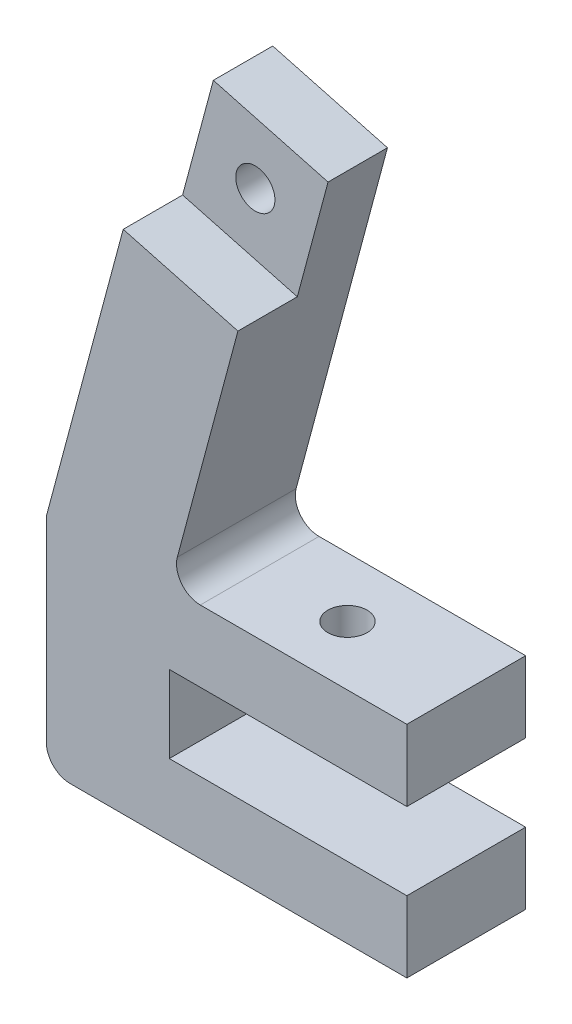
SolidWorks part; units mm, degrees
ref_plane "前视基准面" through (0, 0, 0) normal (0, 0, 1) x (1, 0, 0)
ref_plane "上视基准面" through (0, 0, 0) normal (0, 1, 0) x (1, 0, 0)
ref_plane "右视基准面" through (0, 0, 0) normal (1, 0, 0) x (0, 0, -1)
other "Configuration Table"
sketch "草图1" plane through (0, 0, 0) normal (0, 0, 1) x (1, 0, 0)
  line L0 (0, 0) -> (0, 6)
  line L1 (0, 6) -> (-20, 6)
  line L2 (-20, 6) -> (-20, 12.5)
  line L3 (-20, 12.5) -> (0, 12.5)
  line L4 (0, 12.5) -> (0, 18.5)
  line L5 (0, 18.5) -> (-20, 18.5)
  line L6 (-20, 18.5) -> (-11.6348, 49.7192)
  line L7 (-11.6348, 49.7192) -> (-21.2941, 52.3074)
  line L8 (-21.2941, 52.3074) -> (-30.3528, 18.5)
  line L9 (-30.3528, 18.5) -> (-30.3528, 0)
  line L10 (-30.3528, 0) -> (0, 0)
  point P9 (-25.3563, 18.5)
  point P13 (0, 0)
  dimension "D1" = 6
  dimension "D2" = 6
  dimension "D3" = 6.5
  dimension "D4" = 75
  dimension "D5" = 10
  dimension "D6" = 20
  dimension "D7" = 20
  dimension "D8" = 35
extrude "凸台-拉伸1" add sketch "草图1" along normal blind 10
sketch "草图2" plane through (0, 0, 10) normal (0, 0, 1) x (1, 0, 0)
  line L0 (-21.2941, 52.3074) -> (-11.6348, 49.7192)
  line L1 (-11.6348, 49.7192) -> (-14.223, 40.06)
  line L2 (-20, 18.5) -> (-11.6348, 49.7192) construction
  line L3 (-14.223, 40.06) -> (-23.8823, 42.6481)
  line L4 (-21.2941, 52.3074) -> (-30.3528, 18.5) construction
  line L5 (-23.8823, 42.6481) -> (-21.2941, 52.3074)
  dimension "D1" = 10
extrude "切除-拉伸1" cut sketch "草图2" against normal blind 5
fillet "圆角1" radius 2 1 edges at (-20, 18.5, 5)
sketch "草图12" plane through (0, 18.5, 0) normal (0, 1, 0) x (1, 0, 0)
  line L0 (0, 0) -> (0, -10) construction
  line L1 (0, -5) -> (-10, -5) construction
  circle A0 centre (-10, -5) radius 1
hole_wizard "M4 螺纹孔1" positions "草图17" profile "草图19" tap size "M4" standard "ISO" end condition up to next
sketch "草图17" plane through (0, 18.5, 0) normal (0, 1, 0) x (1, 0, 0)
  point P0 (-10, -5)
sketch "草图19" plane through (-10, 18.5, 5) normal (1, 0, 0) x (0, 0, 1)
  line L0 (0, 0) -> (0, 6)
  line L1 (0, 6) -> (1.65, 6)
  line L2 (1.65, 6) -> (1.65, 0)
  line L5 (1.65, 0) -> (0, 0)
  line L11 (0, -6.35) -> (0, 107.95) construction
  dimension "通孔螺纹孔钻头直径" = 3.3
  dimension "通孔螺纹孔钻头深度" = 6
sketch "草图20" plane through (0, 0, 5) normal (0, 0, 1) x (1, 0, 0)
  line L0 (-21.2941, 52.3074) -> (-14.223, 40.06) construction
  point P6 (0, 0)
hole_wizard "M4 螺纹孔2" positions "草图21" profile "草图22" tap size "M4" standard "ISO" end condition through all
sketch "草图21" plane through (0, 0, 5) normal (0, 0, 1) x (1, 0, 0)
  line L0 (-21.2941, 52.3074) -> (-14.223, 40.06) construction
  point P0 (-17.7586, 46.1837)
sketch "草图22" plane through (-17.7586, 46.1837, 5) normal (1, 0, 0) x (0, -1, 0)
  line L0 (0, 0) -> (0, 5)
  line L1 (0, 5) -> (1.65, 5)
  line L2 (1.65, 5) -> (1.65, 0)
  line L5 (1.65, 0) -> (0, 0)
  line L11 (0, -6.35) -> (0, 107.95) construction
  dimension "通孔螺纹孔钻头直径" = 3.3
  dimension "通孔螺纹孔钻头深度" = 5
fillet "圆角2" radius 2 1 edges at (-30.3528, 0, 5)
sketch "草图23" plane through (0, 0, 0) normal (0, 0, -1) x (-1, 0, 0)
  line L0 (21.2941, 52.3074) -> (14.223, 40.06) construction
  circle A0 centre (17.7586, 46.1837) radius 4
extrude "切除-拉伸3" cut sketch "草图23" against normal blind 1
